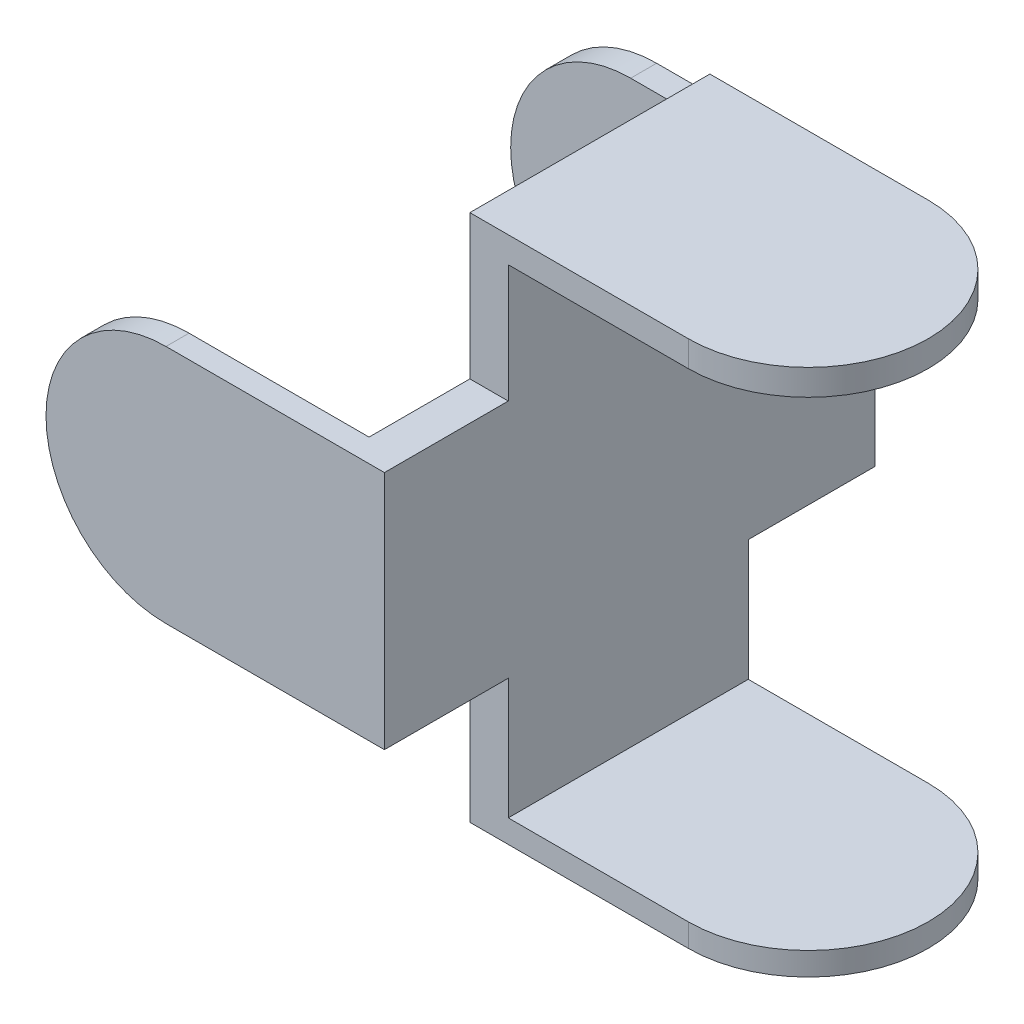
SolidWorks part; units mm, degrees
material "Окись алюминия"
ref_plane "Спереди" through (0, 0, 0) normal (0, 0, 1) x (1, 0, 0)
ref_plane "Сверху" through (0, 0, 0) normal (0, 1, 0) x (1, 0, 0)
ref_plane "Справа" through (0, 0, 0) normal (1, 0, 0) x (0, 0, -1)
other "Configuration Table"
sketch "Эскиз5" plane through (0, 0, 0) normal (0, 0, 1) x (1, 0, 0)
  line L0 (0, 0) -> (22.75, 0) construction
  line L1 (0, 12.5) -> (22.75, 12.5)
  line L2 (22.75, 12.5) -> (22.75, -12.5)
  line L3 (22.75, -12.5) -> (0, -12.5)
  arc A0 (0, 12.5) -> (0, -12.5) centre (0, 0) ccw
  dimension "D2" = 25
  dimension "D1" = 22.75
extrude "Бобышка-Вытянуть5" add sketch "Эскиз5" along normal blind 25.4 and the other way blind 25.7 contours A0 L3 L2 L1
sketch "Эскиз6" plane through (0, 0, 0) normal (0, 0, 1) x (1, 0, 0)
  line L0 (0, 12.5) -> (18.75, 12.5)
  line L1 (0, 12.5) -> (22.75, 12.5) construction
  line L2 (18.75, 12.5) -> (18.75, -12.5)
  line L3 (22.75, -12.5) -> (0, -12.5) construction
  line L4 (18.75, -12.5) -> (0, -12.5)
  line L5 (22.75, 12.5) -> (22.75, -12.5) construction
  arc A0 (0, 12.5) -> (0, -12.5) centre (0, 0) ccw construction
  arc A1 (0, 12.5) -> (0, -12.5) centre (0, 0) ccw
  dimension "D1" = 4
extrude "Вырез-Вытянуть1" cut sketch "Эскиз6" along normal offset from surface 2.4 and the other way offset from surface (23 mm away) 2.7 contours L4 A1 L0 L2 up to face at (8.25, 0, 25.4) other way up to face at (8.25, 0, -25.7)
sketch "Эскиз7" plane through (0, 0, 0) normal (0, 1, 0) x (1, 0, 0)
  line L0 (0, 0) -> (41.5, 0) construction
  line L1 (41.5, 12.5) -> (18.75, 12.5)
  line L2 (18.75, -23) -> (18.75, 23) construction
  line L3 (18.75, 12.5) -> (18.75, -12.5)
  line L4 (18.75, -12.5) -> (41.5, -12.5)
  arc A0 (41.5, -12.5) -> (41.5, 12.5) centre (41.5, 0) ccw
  dimension "D2" = 25
  dimension "D1" = 41.5
extrude "Бобышка-Вытянуть6" add sketch "Эскиз7" along normal mid plane 55 contours L1 L3 L4 A0
sketch "Эскиз8" plane through (0, 0, 0) normal (0, 1, 0) x (1, 0, 0)
  line L0 (41.5, 12.5) -> (22.75, 12.5)
  line L1 (22.75, 12.5) -> (22.75, -12.5)
  line L2 (22.75, -12.5) -> (41.5, -12.5)
  arc A0 (41.5, -12.5) -> (41.5, 12.5) centre (41.5, 0) ccw construction
  arc A1 (41.5, -12.5) -> (41.5, 12.5) centre (41.5, 0) ccw
extrude "Вырез-Вытянуть2" cut sketch "Эскиз8" against normal offset from surface 2.4 and the other way offset from surface (24.8 mm away) 2.7 contours L2 A1 L0 L1 up to face at (33.25, -27.5, 0) other way up to face at (33.25, 27.5, 0)
sketch "Эскиз9" plane through (0, 0, 0) normal (0, 1, 0) x (1, 0, 0)
  line L0 (0, 0) -> (0, 23) construction
  line L1 (0, 0) -> (0, -23) construction
sketch "Эскиз10" plane through (0, 0, 0) normal (0, 0, 1) x (1, 0, 0)
  line L0 (41.5, 24.8) -> (41.5, 0) construction
  line L1 (41.5, 0) -> (41.5, -25.1) construction
  point P3 (0, 0)
  dimension "D1" = 24.8
  dimension "D2" = 25.1
